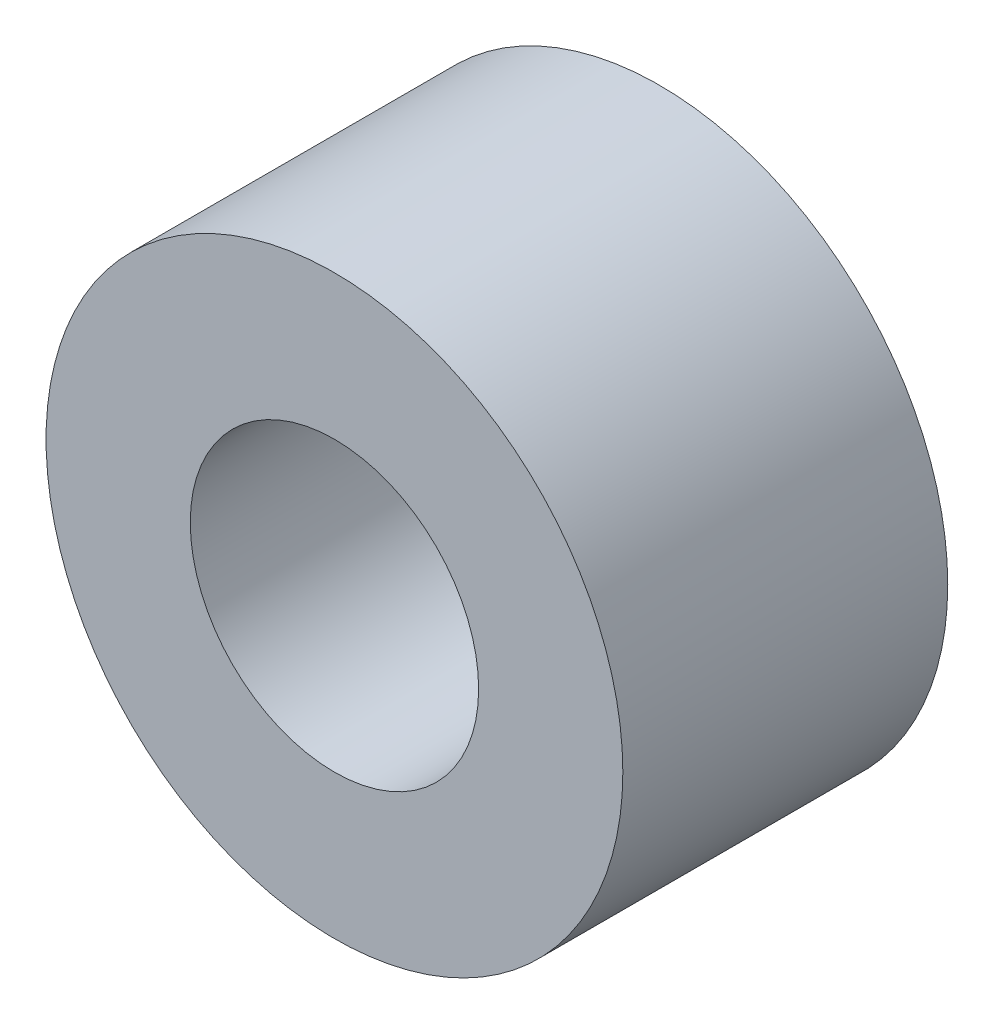
SolidWorks part; units mm, degrees
ref_plane "Front Plane" through (0, 0, 0) normal (0, 0, 1) x (1, 0, 0)
ref_plane "Top Plane" through (0, 0, 0) normal (0, 1, 0) x (1, 0, 0)
ref_plane "Right Plane" through (0, 0, 0) normal (1, 0, 0) x (0, 0, -1)
sketch "Sketch1" plane through (0, 0, 0) normal (0, 0, 1) x (1, 0, 0)
  circle A0 centre (0, 0) radius 1.5
  circle A1 centre (0, 0) radius 3
  dimension "D1" = 3
  dimension "D2" = 6
extrude "Boss-Extrude1" add sketch "Sketch1" along normal blind 3.38
